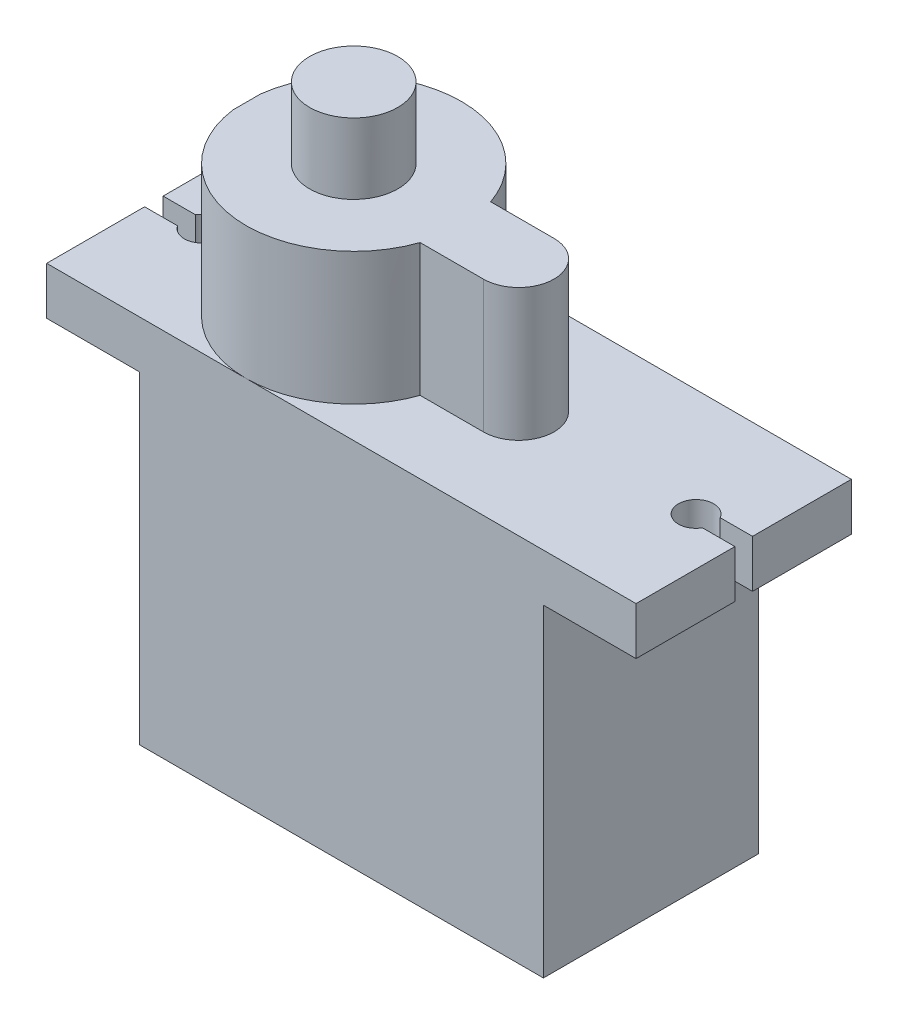
SolidWorks part; units mm, degrees
ref_plane "Front Plane" through (0, 0, 0) normal (0, 0, 1) x (1, 0, 0)
ref_plane "Top Plane" through (0, 0, 0) normal (0, 1, 0) x (1, 0, 0)
ref_plane "Right Plane" through (0, 0, 0) normal (1, 0, 0) x (0, 0, -1)
sketch "Sketch1" plane through (0, 0, 0) normal (0, 0, 1) x (1, 0, 0)
  line L0 (-5.25, 21) -> (-5.25, 18.3)
  line L1 (0, 0) -> (22.9, 0)
  line L2 (0, 0) -> (0, 18.3)
  line L3 (0, 28.5) -> (22.9, 28.5)
  line L4 (22.9, 0) -> (22.9, 18.3)
  line L5 (-5.25, 18.3) -> (0, 18.3)
  line L6 (28.15, 18.3) -> (28.15, 21)
  line L7 (-5.25, 21) -> (0, 21)
  line L8 (0, 21) -> (0, 28.5)
  line L9 (22.9, 21) -> (28.15, 21)
  line L10 (22.9, 18.3) -> (28.15, 18.3)
  line L11 (22.9, 21) -> (22.9, 28.5)
  dimension "D1" = 22.9
  dimension "D2" = 18.3
  dimension "D3" = 2.7
  dimension "D4" = 5.25
  dimension "D5" = 5.25
  dimension "D6" = 7.5
extrude "Boss-Extrude1" add sketch "Sketch1" along normal blind 12.2
sketch "Sketch2" plane through (0, 21, 0) normal (0, 1, 0) x (1, 0, 0)
  line L0 (28.15, -12.2) -> (28.15, 0) construction
  line L1 (-5.25, -12.2) -> (-5.25, 0) construction
  line L2 (0, -12.2) -> (-5.25, -12.2) construction
  line L3 (28.15, -12.2) -> (22.9, -12.2) construction
  circle A0 centre (-2.55, -6.1) radius 1
  circle A1 centre (25.45, -6.1) radius 1
  dimension "D1" = 2
  dimension "D2" = 2
  dimension "D3" = 2.7
  dimension "D4" = 2.7
  dimension "D5" = 6.1
  dimension "D6" = 6.1
extrude "Cut-Extrude1" cut sketch "Sketch2" against normal blind 12.5
sketch "Sketch3" plane through (0, 28.5, 0) normal (0, 1, 0) x (1, 0, 0)
  line L0 (22.9, -12.2) -> (0, -12.2) construction
  circle A0 centre (6.05, -6.1) radius 2.5
  circle A1 centre (-2.55, -6.1) radius 1 construction
  dimension "D3" = 5
  dimension "D1" = 8.6
  dimension "D2" = 6.1
extrude "Boss-Extrude2" add sketch "Sketch3" along normal blind 4
sketch "Sketch4" plane through (0, 28.5, 0) normal (0, 1, 0) x (1, 0, 0)
  line L0 (22.9, -12.2) -> (0, -12.2) construction
  line L1 (0, 0) -> (17.4, 0)
  line L2 (0, 0) -> (0, -12.2)
  line L3 (0, -12.2) -> (17.4, -12.2)
  line L4 (17.4, 0) -> (17.4, -12.2) construction
  line L5 (15.4, -8.1) -> (11.8128, -8.1)
  line L6 (15.4, -4.1) -> (11.8128, -4.1)
  line L7 (22.9, -12.2) -> (22.9, 0) construction
  line L8 (17.4, 0) -> (22.9, 0)
  line L9 (22.9, 0) -> (22.9, -12.2)
  line L10 (22.9, -12.2) -> (17.4, -12.2)
  arc A0 (11.8128, -4.1) -> (11.8128, -8.1) centre (6.05, -6.1) ccw
  arc A1 (15.4, -8.1) -> (15.4, -4.1) centre (15.4, -6.1) ccw
  line M10 (22.9, 0) -> (0, 0)
  line M11 (0, 0) -> (0, -12.2)
  line M12 (0, -12.2) -> (22.9, -12.2)
  line M13 (22.9, -12.2) -> (22.9, 0)
  dimension "D2" = 4
  dimension "D4" = 12.2
  dimension "D1" = 5.5
  dimension "D3" = 6.1
extrude "Cut-Extrude2" cut sketch "Sketch4" against normal blind 7.5 contours L4 M10 M12 M13 | L4 A1 L5 A0 L3 | L4 A0 L6 A1 M10 | A0 L1 M11 | A0 M11 M12
sketch "Sketch5" plane through (0, 21, 0) normal (0, 1, 0) x (1, 0, 0)
  line L0 (-5.25, -12.2) -> (-5.25, 0) construction
  line L1 (-5.25, -5.6) -> (-2.4779, -5.6)
  line L2 (-5.25, -5.6) -> (-5.25, -6.65)
  line L3 (-5.25, -6.65) -> (-2.4779, -6.65)
  line L4 (-2.4779, -5.6) -> (-2.4779, -6.65)
  line L5 (28.15, -12.2) -> (28.15, 0) construction
  line L6 (25.5364, -5.6) -> (28.15, -5.6)
  line L7 (25.5364, -5.6) -> (25.5364, -6.6)
  line L8 (25.5364, -6.6) -> (28.15, -6.6)
  line L9 (28.15, -5.6) -> (28.15, -6.6)
  circle A0 centre (-2.55, -6.1) radius 1 construction
  circle A1 centre (25.45, -6.1) radius 1 construction
  dimension "D1" = 0.5
  dimension "D2" = 0.55
  dimension "D3" = 0.5
  dimension "D4" = 0.5
extrude "Cut-Extrude3" cut sketch "Sketch5" against normal blind 7.5
